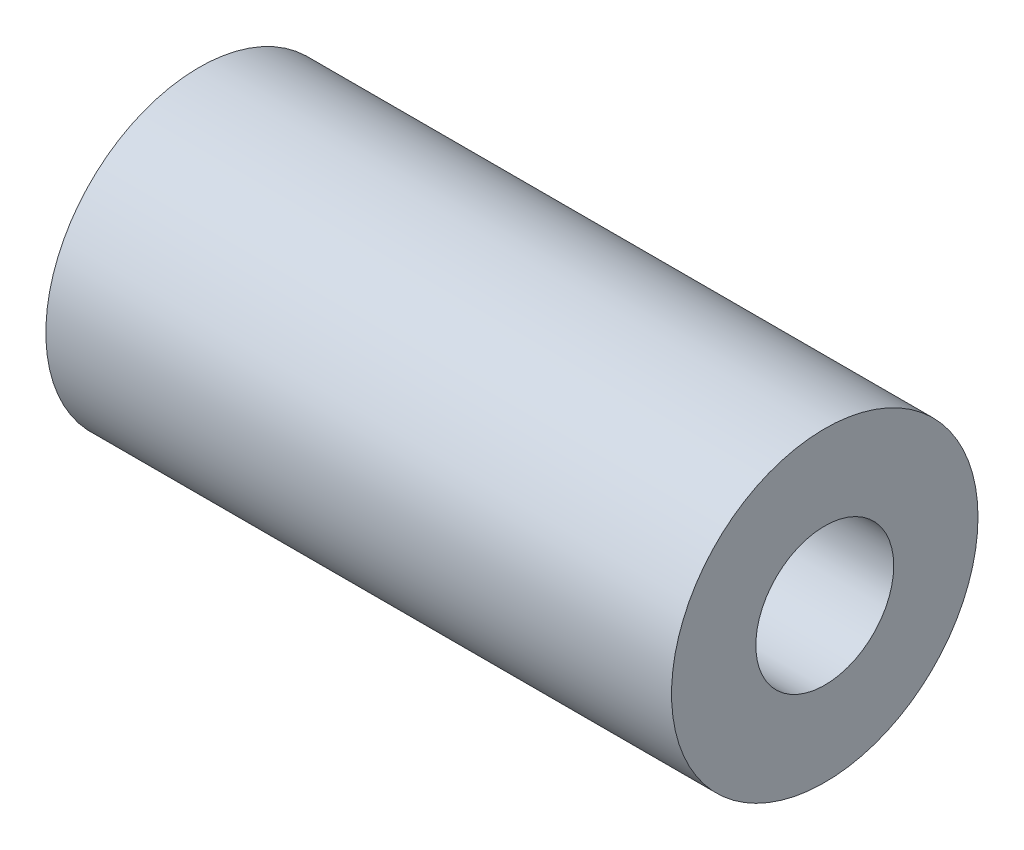
SolidWorks part; units mm, degrees
ref_plane "前视基准面" through (0, 0, 0) normal (0, 0, 1) x (1, 0, 0)
ref_plane "上视基准面" through (0, 0, 0) normal (0, 1, 0) x (1, 0, 0)
ref_plane "右视基准面" through (0, 0, 0) normal (1, 0, 0) x (0, 0, -1)
sketch "草图1" plane through (0, 0, 0) normal (1, 0, 0) x (0, 0, -1)
  circle A0 centre (0, 0) radius 2.7
  circle A1 centre (0, 0) radius 6
  dimension "D1" = 12
  dimension "D2" = 5.4
extrude "凸台-拉伸1" add sketch "草图1" along normal blind 24.5
